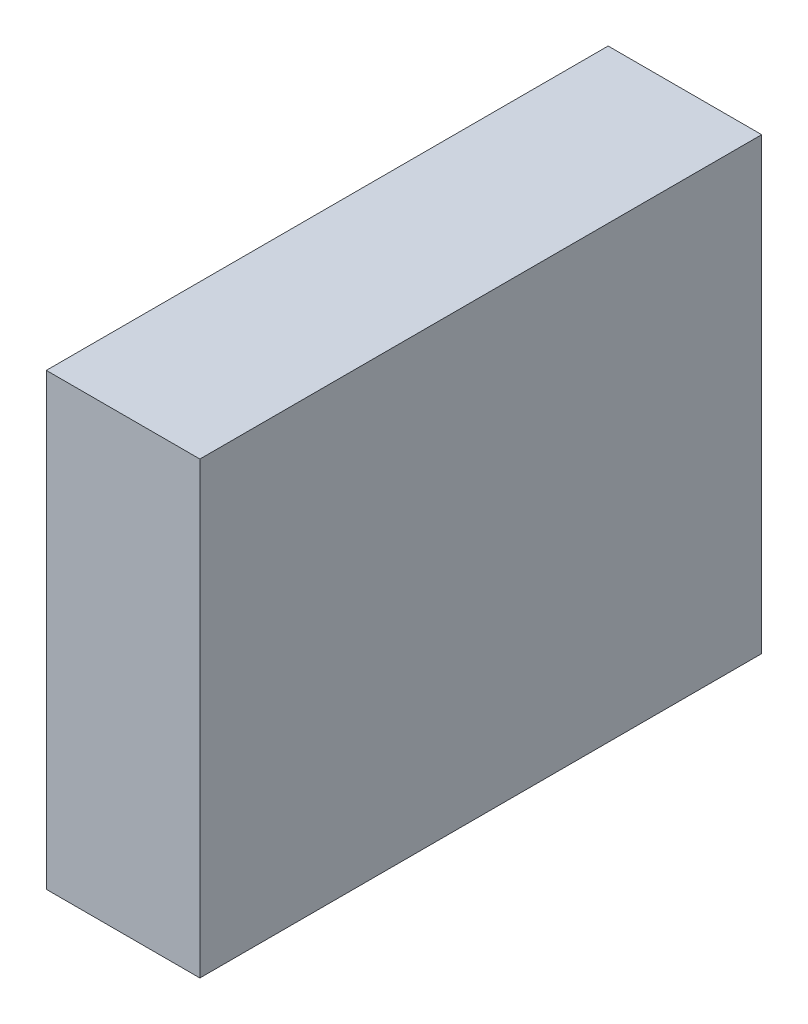
SolidWorks part; units mm, degrees
material "Corrugated Paper"
ref_plane "Front Plane" through (0, 0, 0) normal (0, 0, 1) x (1, 0, 0)
ref_plane "Top Plane" through (0, 0, 0) normal (0, 1, 0) x (1, 0, 0)
ref_plane "Right Plane" through (0, 0, 0) normal (1, 0, 0) x (0, 0, -1)
sketch "Sketch1" plane through (0, 0, 0) normal (1, 0, 0) x (0, 0, -1)
  line L1 (-7.5, -6) -> (7.5, -6)
  line L2 (-7.5, -6) -> (-7.5, 6)
  line L3 (-7.5, 6) -> (7.5, 6)
  line L4 (7.5, -6) -> (7.5, 6)
  line L5 (-7.5, -6) -> (7.5, 6) construction
  line L6 (-7.5, 6) -> (7.5, -6) construction
  point P0 (0, 0)
  dimension "D1" = 12
  dimension "D2" = 15
extrude "Boss-Extrude1" add sketch "Sketch1" along normal blind 4.1
